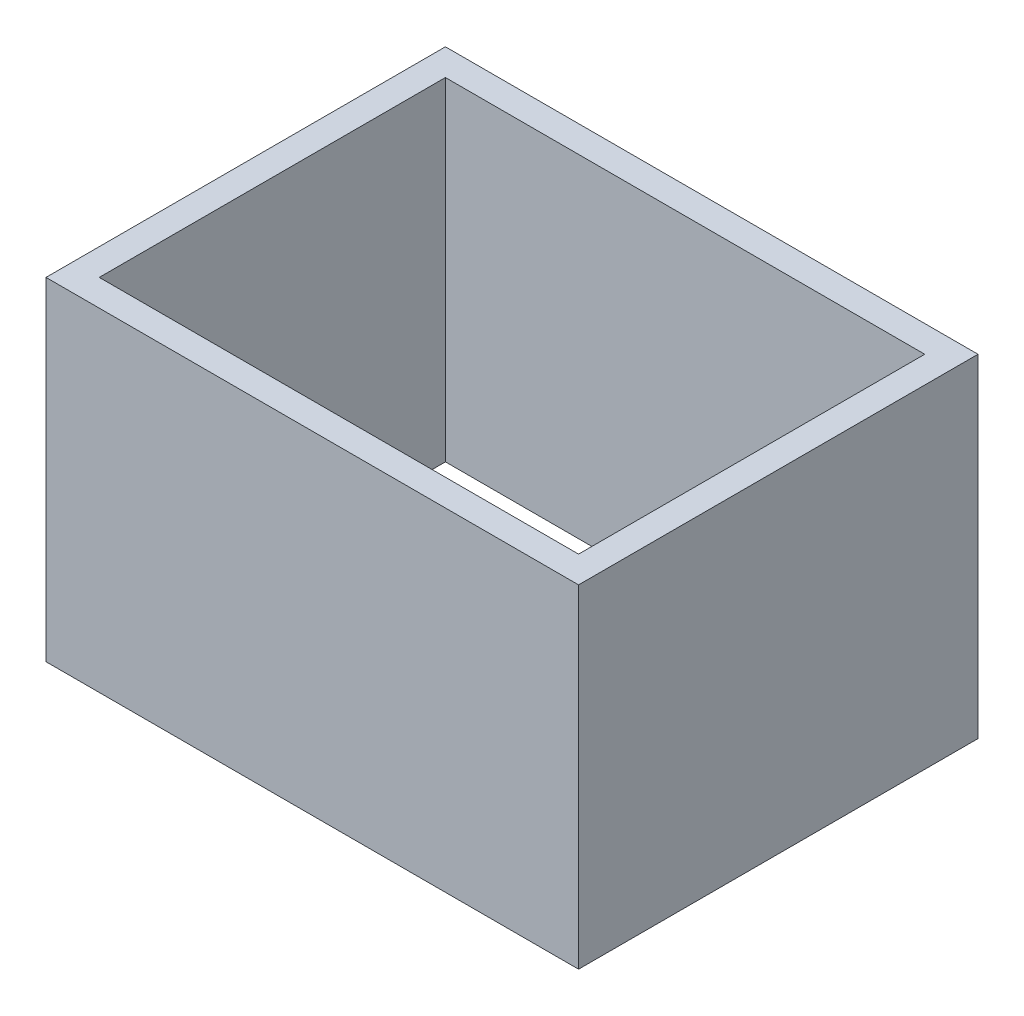
SolidWorks part; units mm, degrees
ref_plane "Ebene vorne" through (0, 0, 0) normal (0, 0, 1) x (1, 0, 0)
ref_plane "Ebene oben" through (0, 0, 0) normal (0, 1, 0) x (1, 0, 0)
ref_plane "Ebene rechts" through (0, 0, 0) normal (1, 0, 0) x (0, 0, -1)
sketch "Skizze2" plane through (0, 0, 0) normal (0, 1, 0) x (1, 0, 0)
  line L0 (200, 200) -> (200, 2800)
  line L1 (0, 0) -> (4000, 0)
  line L2 (0, 0) -> (0, 3000)
  line L3 (0, 3000) -> (4000, 3000)
  line L4 (4000, 0) -> (4000, 3000)
  line L5 (200, 2800) -> (3800, 2800)
  line L6 (3800, 200) -> (3800, 2800)
  line L7 (200, 200) -> (3800, 200)
  dimension "D1" = 4000
  dimension "D2" = 3000
  dimension "D3" = 200
extrude "Aufsatz-Linear austragen1" add sketch "Skizze2" along normal blind 2500
